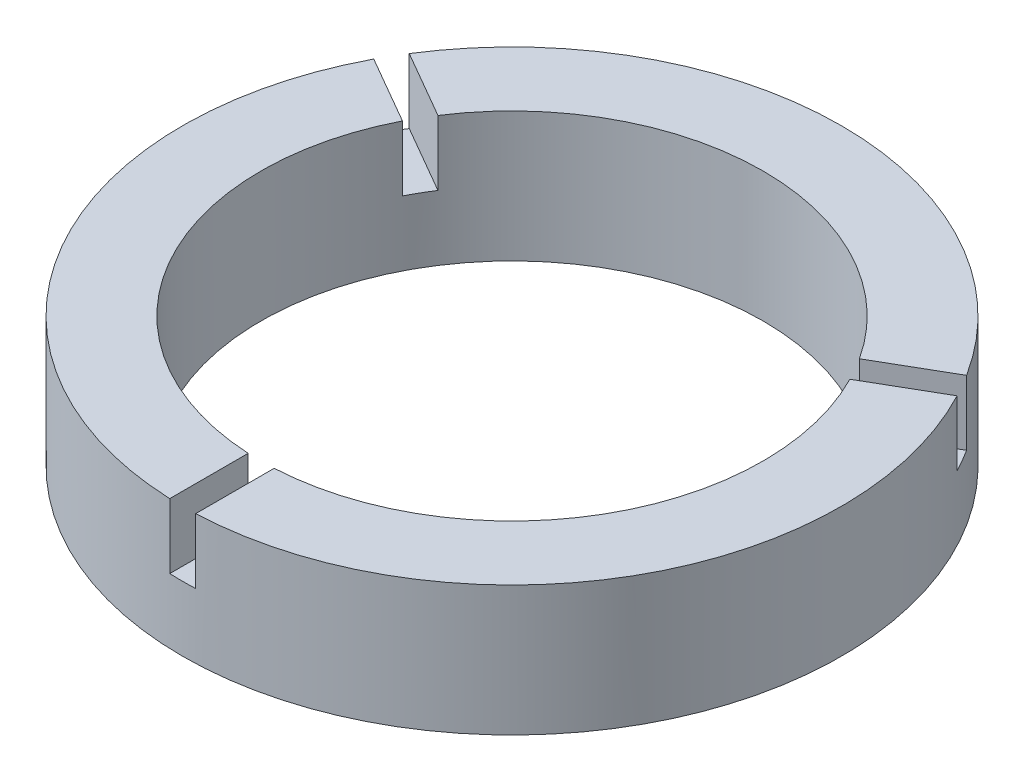
SolidWorks part; units mm, degrees
ref_plane "Front Plane" through (0, 0, 0) normal (0, 0, 1) x (1, 0, 0)
ref_plane "Top Plane" through (0, 0, 0) normal (0, 1, 0) x (1, 0, 0)
ref_plane "Right Plane" through (0, 0, 0) normal (1, 0, 0) x (0, 0, -1)
sketch "Sketch1" plane through (0, 0, 0) normal (0, 1, 0) x (1, 0, 0)
  circle A0 centre (0, 0) radius 38.05
  circle A1 centre (0, 0) radius 29
  dimension "D1" = 76.1
  dimension "D2" = 58
extrude "Boss-Extrude1" add sketch "Sketch1" along normal blind 15
sketch "Sketch3" plane through (0, 15, 0) normal (0, 1, 0) x (1, 0, 0)
  line L0 (0, -20) -> (0, -52.802)
  line L1 (-17.3205, 10) -> (-45.7279, 26.401)
  line L2 (17.3205, 10) -> (45.7279, 26.401)
  circle A0 centre (0, 0) radius 20
  circle A1 centre (0, 0) radius 52.802
  point P12 (0, 0)
  dimension "D1" = 40
  dimension "D2" = 105.604
  dimension "D3" = 3
extrude "Cut-Extrude-Thin1" cut sketch "Sketch3" against normal blind 7.5 thin thin type mid plane wall 3
